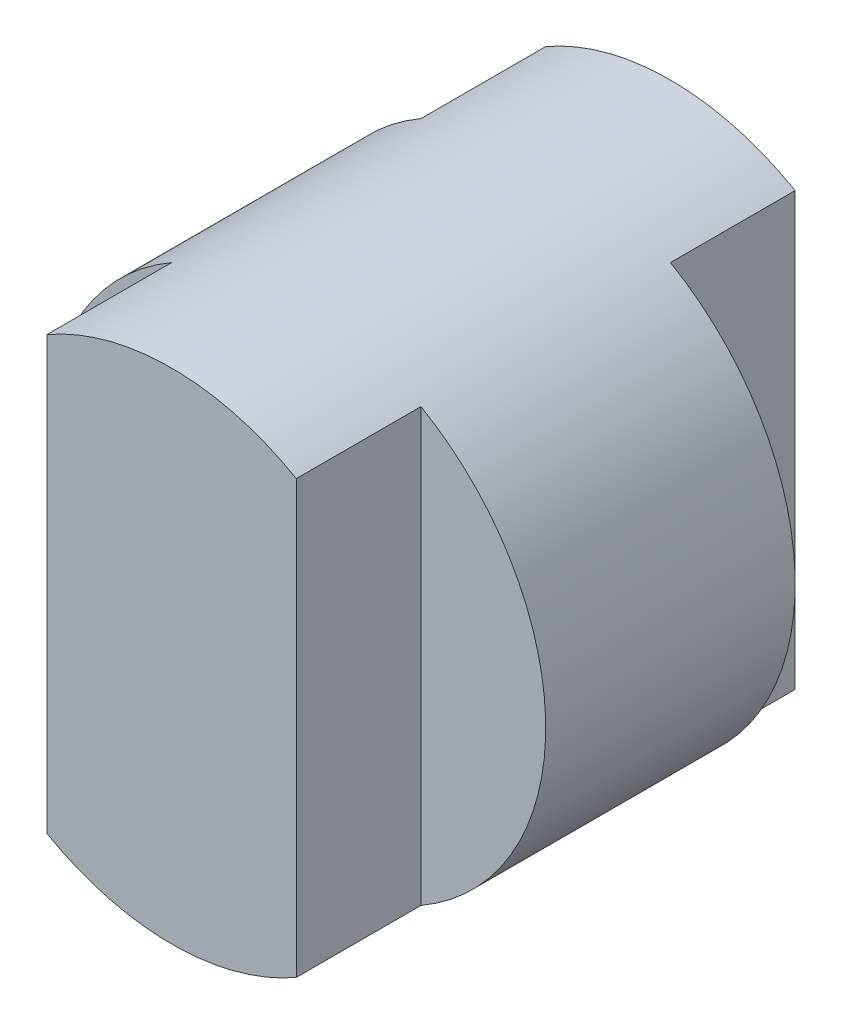
SolidWorks part; units mm, degrees
ref_plane "Front" through (0, 0, 0) normal (0, 0, 1) x (1, 0, 0)
ref_plane "Top" through (0, 0, 0) normal (0, 1, 0) x (1, 0, 0)
ref_plane "Right" through (0, 0, 0) normal (1, 0, 0) x (0, 0, -1)
sketch "Sketch1" plane through (0, 0, 0) normal (0, 0, 1) x (1, 0, 0)
  circle A0 centre (0, 0) radius 2
  dimension "D1" = 4
extrude "Boss-Extrude1" add sketch "Sketch1" along normal blind 4
sketch "Sketch2" plane through (0, 0, 0) normal (0, 1, 0) x (1, 0, 0)
  line L0 (2, -3) -> (1, -3)
  line L1 (2, -4) -> (2, 0) construction
  line L2 (1, -3) -> (1, -4.2215)
  line L3 (1, -4.2215) -> (-1, -4.2646)
  line L4 (-1, -4.2646) -> (-1, -3)
  line L5 (-1, -3) -> (-2.3139, -3)
  line L6 (-2.3139, -3) -> (-2.3139, -1)
  line L7 (-2.3139, -1) -> (-1, -1)
  line L8 (-1, -1) -> (-1, 0.234)
  line L9 (-1, 0.234) -> (-2.5868, 0.1999)
  line L10 (-2.5868, 0.1999) -> (-2.4898, -4.307)
  line L11 (-2.4898, -4.307) -> (2, -4.619)
  line L12 (2, -4.619) -> (2.5546, -4.2215)
  line L13 (2.5546, -4.2215) -> (2, -3)
  line L14 (-2, -4) -> (2, -4) construction
  line L15 (-2, 0) -> (-2, -4) construction
  line L16 (2, 0) -> (-2, 0) construction
  dimension "D1" = 1
  dimension "D2" = 1
  dimension "D3" = 1.2215
  dimension "D4" = 1
  dimension "D5" = 1
  dimension "D6" = 1
  dimension "D7" = 1
extrude "Cut-Extrude1" cut sketch "Sketch2" against normal mid plane 10
sketch "Sketch3" plane through (0, 0, 0) normal (0, 1, 0) x (1, 0, 0)
  line L1 (2, 0) -> (1, 0)
  line L2 (2, 0) -> (2, -1)
  line L3 (2, -1) -> (1, -1)
  line L4 (1, 0) -> (1, -1)
  dimension "D1" = 1
  dimension "D2" = 1
extrude "Cut-Extrude2" cut sketch "Sketch3" against normal mid plane 10
